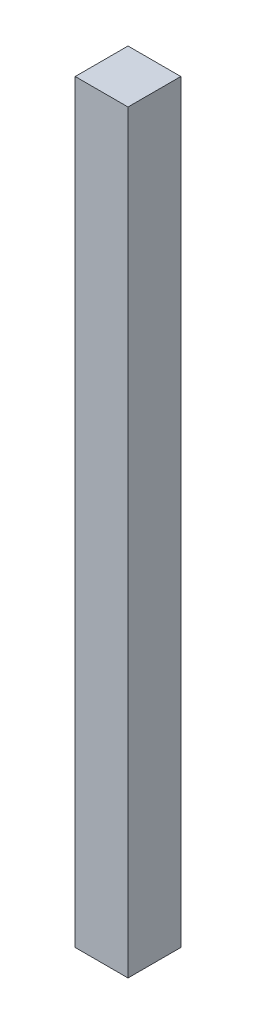
SolidWorks part; units mm, degrees
ref_plane "Front Plane" through (0, 0, 0) normal (0, 0, 1) x (1, 0, 0)
ref_plane "Top Plane" through (0, 0, 0) normal (0, 1, 0) x (1, 0, 0)
ref_plane "Right Plane" through (0, 0, 0) normal (1, 0, 0) x (0, 0, -1)
sketch "Sketch1" plane through (0, 0, 0) normal (0, 1, 0) x (1, 0, 0)
  line L1 (0, 0) -> (4.9, 0)
  line L2 (0, 0) -> (0, 4.9)
  line L3 (0, 4.9) -> (4.9, 4.9)
  line L4 (4.9, 0) -> (4.9, 4.9)
  dimension "D1" = 4.9
extrude "Boss-Extrude1" add sketch "Sketch1" along normal blind 70
